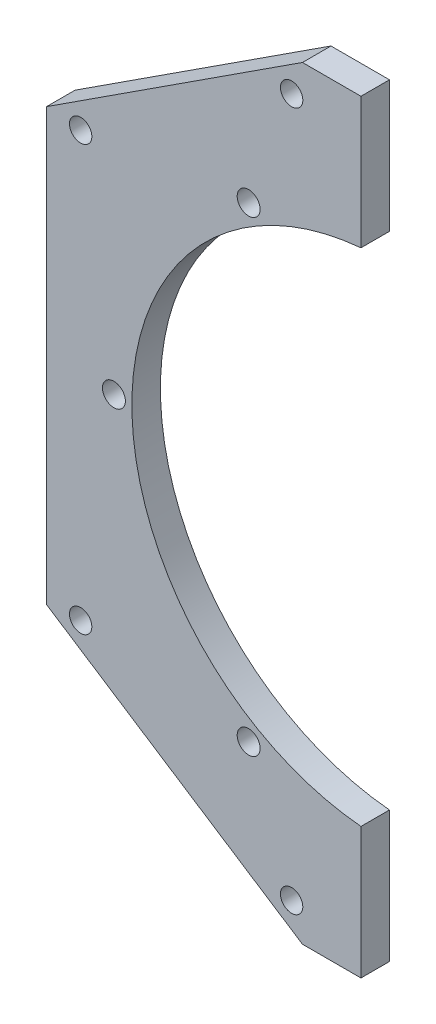
SolidWorks part; units mm, degrees
material "6061-T6 (SS)"
ref_plane "Front Plane" through (0, 0, 0) normal (0, 0, 1) x (1, 0, 0)
ref_plane "Top Plane" through (0, 0, 0) normal (0, 1, 0) x (1, 0, 0)
ref_plane "Right Plane" through (0, 0, 0) normal (1, 0, 0) x (0, 0, -1)
sketch "Sketch1" plane through (0, 0, 0) normal (0, 0, 1) x (1, 0, 0)
  line L0 (-5, 115.4469) -> (-5, -74.6946) construction
  line L1 (0, 0) -> (0, -61.4445) construction
  line L2 (-75, 48) -> (-18.025, 85)
  line L3 (-20.4359, 77.7557) -> (-67.4014, 47.2559) construction
  line L4 (0, 0) -> (41.4814, 0) construction
  line L5 (-75, 48) -> (-75, 0)
  line L6 (-5, 85) -> (-18.025, 85)
  line L7 (-5, 85) -> (-5, 0)
  line L8 (-5, 0) -> (-75, 0)
  line L9 (-46.5125, 66.5) -> (-57.535, 83.4731) construction
  circle A0 centre (0, 0) radius 21.275 construction
  circle A1 centre (0, 0) radius 71.275 construction
  point P17 (-43.9187, 62.5058)
  dimension "D1" = 142.55
  dimension "D2" = 42.55
  dimension "D3" = 5
  dimension "D4" = 33
  dimension "D5" = 70
  dimension "D6" = 85
  dimension "D7" = 48
  dimension "D8" = 4.7625
  dimension "D9" = 56
extrude "Boss-Extrude1" add sketch "Sketch1" along normal blind 6.35
hole_wizard "#10 Clearance Hole1" positions "Sketch3" profile "Sketch2" hole size "#10" standard "ANSI Inch"
sketch "Sketch3" plane through (0, 0, 0) normal (0, 0, -1) x (-1, 0, 0)
  point P0 (20.4359, 77.7557)
  point P2 (67.4014, 47.2559)
sketch "Sketch2" plane through (-20.4359, 77.7557, 0) normal (1, 0, 0) x (0, 1, 0)
  line L0 (0, 0) -> (0, 137.3857)
  line L1 (0, 137.3857) -> (2.4892, 135.89)
  line L2 (2.4892, 135.89) -> (2.4892, 0)
  line L5 (2.4892, 0) -> (0, 0)
  line L10 (0, 137.3857) -> (-2.4892, 135.89) construction
  line L11 (0, -6.35) -> (0, 107.95) construction
  dimension "Hole Dia." = 4.9784
  dimension "Hole Depth" = 135.89
  dimension "Drill Angle" = 118
sketch "Sketch4" plane through (0, 0, 0) normal (0, 0, -1) x (-1, 0, 0)
  circle A0 centre (0, 0) radius 56
  dimension "D1" = 112
extrude "Cut-Extrude1" cut sketch "Sketch4" against normal through all
mirror "Mirror1" about plane through (0, 0, 0) normal (0, 1, 0) of bodies 103
hole_wizard "#10 Clearance Hole2" positions "Sketch6" profile "Sketch5" hole size "#10" standard "ANSI Inch" end condition through all
sketch "Sketch6" plane through (0, 0, 6.35) normal (0, 0, 1) x (1, 0, 0)
  line L0 (0, 0) -> (0, 43.3097) construction
  line L1 (0, 0) -> (-20.5352, 35.5679) construction
  point P0 (-30, 51.9615)
  dimension "D1" = 30
  dimension "D2" = 60
sketch "Sketch5" plane through (-30, 51.9615, 6.35) normal (1, 0, 0) x (0, -1, 0)
  line L0 (0, 0) -> (0, 6.35)
  line L1 (0, 6.35) -> (2.5527, 6.35)
  line L2 (2.5527, 6.35) -> (2.5527, 0)
  line L5 (2.5527, 0) -> (0, 0)
  line L11 (0, -6.35) -> (0, 107.95) construction
  dimension "Thru Hole Dia." = 5.1054
  dimension "Thru Hole Depth" = 6.35
pattern_circular "CirPattern1" count 3 every 60 about axis through (0, 0, 0) along (0, 0, 1) of "#10 Clearance Hole2"
